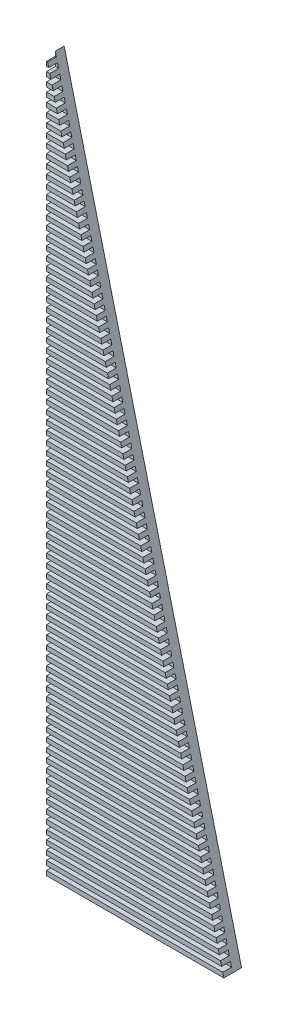
SolidWorks part; units mm, degrees
ref_plane "Front Plane" through (0, 0, 0) normal (0, 0, 1) x (1, 0, 0)
ref_plane "Top Plane" through (0, 0, 0) normal (0, 1, 0) x (1, 0, 0)
ref_plane "Right Plane" through (0, 0, 0) normal (1, 0, 0) x (0, 0, -1)
sketch "Sketch2" plane through (0, 0, 0) normal (0, 0, 1) x (1, 0, 0)
  line L0 (-53.1415, -19.5554) -> (-13.1415, -19.5554)
  line L1 (-53.1415, -19.5554) -> (-53.1415, 140.4446)
  line L2 (-53.1415, 140.4446) -> (-13.1415, -19.5554)
  dimension "D1" = 40
  dimension "D2" = 160
extrude "Boss-Extrude4" add sketch "Sketch2" along normal blind 2
sketch "Sketch4" plane through (0, 0, 2) normal (0, 0, 1) x (1, 0, 0)
  line L0 (-53.1415, -19.5554) -> (-13.1415, -19.5554)
  line L1 (-13.1415, -19.5554) -> (-53.1415, 140.4446)
  line L2 (-53.1415, 140.4446) -> (-53.1415, -19.5554)
  line L3 (-53.1415, -18.5554) -> (-13.3915, -18.5554)
  line L4 (-53.1415, -17.5554) -> (-13.6415, -17.5554)
  line L5 (-53.1415, -16.5554) -> (-13.8915, -16.5554)
  line L6 (-53.1415, -15.5554) -> (-14.1415, -15.5554)
  line L7 (-53.1415, -14.5554) -> (-14.3915, -14.5554)
  line L8 (-53.1415, -13.5554) -> (-14.6415, -13.5554)
  line L9 (-53.1415, -12.5554) -> (-14.8915, -12.5554)
  line L10 (-53.1415, -11.5554) -> (-15.1415, -11.5554)
  line L11 (-53.1415, -10.5554) -> (-15.3915, -10.5554)
  line L12 (-53.1415, -9.5554) -> (-15.6415, -9.5554)
  line L13 (-53.1415, -8.5554) -> (-15.8915, -8.5554)
  line L14 (-53.1415, -7.5554) -> (-16.1415, -7.5554)
  line L15 (-53.1415, -6.5554) -> (-16.3915, -6.5554)
  line L16 (-53.1415, -5.5554) -> (-16.6415, -5.5554)
  line L17 (-53.1415, -4.5554) -> (-16.8915, -4.5554)
  line L18 (-53.1415, -3.5554) -> (-17.1415, -3.5554)
  line L19 (-53.1415, -2.5554) -> (-17.3915, -2.5554)
  line L20 (-53.1415, -1.5554) -> (-17.6415, -1.5554)
  line L21 (-53.1415, -0.5554) -> (-17.8915, -0.5554)
  line L22 (-53.1415, 0.4446) -> (-18.1415, 0.4446)
  line L23 (-53.1415, 1.4446) -> (-18.3915, 1.4446)
  line L24 (-53.1415, 2.4446) -> (-18.6415, 2.4446)
  line L25 (-53.1415, 3.4446) -> (-18.8915, 3.4446)
  line L26 (-53.1415, 4.4446) -> (-19.1415, 4.4446)
  line L27 (-53.1415, 5.4446) -> (-19.3915, 5.4446)
  line L28 (-53.1415, 6.4446) -> (-19.6415, 6.4446)
  line L29 (-53.1415, 7.4446) -> (-19.8915, 7.4446)
  line L30 (-53.1415, 8.4446) -> (-20.1415, 8.4446)
  line L31 (-53.1415, 9.4446) -> (-20.3915, 9.4446)
  line L32 (-53.1415, 10.4446) -> (-20.6415, 10.4446)
  line L33 (-53.1415, 11.4446) -> (-20.8915, 11.4446)
  line L34 (-53.1415, 12.4446) -> (-21.1415, 12.4446)
  line L35 (-53.1415, 13.4446) -> (-21.3915, 13.4446)
  line L36 (-53.1415, 14.4446) -> (-21.6415, 14.4446)
  line L37 (-53.1415, 15.4446) -> (-21.8915, 15.4446)
  line L38 (-53.1415, 16.4446) -> (-22.1415, 16.4446)
  line L39 (-53.1415, 17.4446) -> (-22.3915, 17.4446)
  line L40 (-53.1415, 18.4446) -> (-22.6415, 18.4446)
  line L41 (-53.1415, 19.4446) -> (-22.8915, 19.4446)
  line L42 (-53.1415, 20.4446) -> (-23.1415, 20.4446)
  line L43 (-53.1415, 21.4446) -> (-23.3915, 21.4446)
  line L44 (-53.1415, 22.4446) -> (-23.6415, 22.4446)
  line L45 (-53.1415, 23.4446) -> (-23.8915, 23.4446)
  line L46 (-53.1415, 24.4446) -> (-24.1415, 24.4446)
  line L47 (-53.1415, 25.4446) -> (-24.3915, 25.4446)
  line L48 (-53.1415, 26.4446) -> (-24.6415, 26.4446)
  line L49 (-53.1415, 27.4446) -> (-24.8915, 27.4446)
  line L50 (-53.1415, 28.4446) -> (-25.1415, 28.4446)
  line L51 (-53.1415, 29.4446) -> (-25.3915, 29.4446)
  line L52 (-53.1415, 30.4446) -> (-25.6415, 30.4446)
  line L53 (-53.1415, 31.4446) -> (-25.8915, 31.4446)
  line L54 (-53.1415, 32.4446) -> (-26.1415, 32.4446)
  line L55 (-53.1415, 33.4446) -> (-26.3915, 33.4446)
  line L56 (-53.1415, 34.4446) -> (-26.6415, 34.4446)
  line L57 (-53.1415, 35.4446) -> (-26.8915, 35.4446)
  line L58 (-53.1415, 36.4446) -> (-27.1415, 36.4446)
  line L59 (-53.1415, 37.4446) -> (-27.3915, 37.4446)
  line L60 (-53.1415, 38.4446) -> (-27.6415, 38.4446)
  line L61 (-53.1415, 39.4446) -> (-27.8915, 39.4446)
  line L62 (-53.1415, 40.4446) -> (-28.1415, 40.4446)
  line L63 (-53.1415, 41.4446) -> (-28.3915, 41.4446)
  line L64 (-53.1415, 42.4446) -> (-28.6415, 42.4446)
  line L65 (-53.1415, 43.4446) -> (-28.8915, 43.4446)
  line L66 (-53.1415, 44.4446) -> (-29.1415, 44.4446)
  line L67 (-53.1415, 45.4446) -> (-29.3915, 45.4446)
  line L68 (-53.1415, 46.4446) -> (-29.6415, 46.4446)
  line L69 (-53.1415, 47.4446) -> (-29.8915, 47.4446)
  line L70 (-53.1415, 48.4446) -> (-30.1415, 48.4446)
  line L71 (-53.1415, 49.4446) -> (-30.3915, 49.4446)
  line L72 (-53.1415, 50.4446) -> (-30.6415, 50.4446)
  line L73 (-53.1415, 51.4446) -> (-30.8915, 51.4446)
  line L74 (-53.1415, 52.4446) -> (-31.1415, 52.4446)
  line L75 (-53.1415, 53.4446) -> (-31.3915, 53.4446)
  line L76 (-53.1415, 54.4446) -> (-31.6415, 54.4446)
  line L77 (-53.1415, 55.4446) -> (-31.8915, 55.4446)
  line L78 (-53.1415, 56.4446) -> (-32.1415, 56.4446)
  line L79 (-53.1415, 57.4446) -> (-32.3915, 57.4446)
  line L80 (-53.1415, 58.4446) -> (-32.6415, 58.4446)
  line L81 (-53.1415, 59.4446) -> (-32.8915, 59.4446)
  line L82 (-53.1415, 60.4446) -> (-33.1415, 60.4446)
  line L83 (-53.1415, 61.4446) -> (-33.3915, 61.4446)
  line L84 (-53.1415, 62.4446) -> (-33.6415, 62.4446)
  line L85 (-53.1415, 63.4446) -> (-33.8915, 63.4446)
  line L86 (-53.1415, 64.4446) -> (-34.1415, 64.4446)
  line L87 (-53.1415, 65.4446) -> (-34.3915, 65.4446)
  line L88 (-53.1415, 66.4446) -> (-34.6415, 66.4446)
  line L89 (-53.1415, 67.4446) -> (-34.8915, 67.4446)
  line L90 (-53.1415, 68.4446) -> (-35.1415, 68.4446)
  line L91 (-53.1415, 69.4446) -> (-35.3915, 69.4446)
  line L92 (-53.1415, 70.4446) -> (-35.6415, 70.4446)
  line L93 (-53.1415, 71.4446) -> (-35.8915, 71.4446)
  line L94 (-53.1415, 72.4446) -> (-36.1415, 72.4446)
  line L95 (-53.1415, 73.4446) -> (-36.3915, 73.4446)
  line L96 (-53.1415, 74.4446) -> (-36.6415, 74.4446)
  line L97 (-53.1415, 75.4446) -> (-36.8915, 75.4446)
  line L98 (-53.1415, 76.4446) -> (-37.1415, 76.4446)
  line L99 (-53.1415, 77.4446) -> (-37.3915, 77.4446)
  line L100 (-53.1415, 78.4446) -> (-37.6415, 78.4446)
  line L101 (-53.1415, 79.4446) -> (-37.8915, 79.4446)
  line L102 (-53.1415, 80.4446) -> (-38.1415, 80.4446)
  line L103 (-53.1415, 81.4446) -> (-38.3915, 81.4446)
  line L104 (-53.1415, 82.4446) -> (-38.6415, 82.4446)
  line L105 (-53.1415, 83.4446) -> (-38.8915, 83.4446)
  line L106 (-53.1415, 84.4446) -> (-39.1415, 84.4446)
  line L107 (-53.1415, 85.4446) -> (-39.3915, 85.4446)
  line L108 (-53.1415, 86.4446) -> (-39.6415, 86.4446)
  line L109 (-53.1415, 87.4446) -> (-39.8915, 87.4446)
  line L110 (-53.1415, 88.4446) -> (-40.1415, 88.4446)
  line L111 (-53.1415, 89.4446) -> (-40.3915, 89.4446)
  line L112 (-53.1415, 90.4446) -> (-40.6415, 90.4446)
  line L113 (-53.1415, 91.4446) -> (-40.8915, 91.4446)
  line L114 (-53.1415, 92.4446) -> (-41.1415, 92.4446)
  line L115 (-53.1415, 93.4446) -> (-41.3915, 93.4446)
  line L116 (-53.1415, 94.4446) -> (-41.6415, 94.4446)
  line L117 (-53.1415, 95.4446) -> (-41.8915, 95.4446)
  line L118 (-53.1415, 96.4446) -> (-42.1415, 96.4446)
  line L119 (-53.1415, 97.4446) -> (-42.3915, 97.4446)
  line L120 (-53.1415, 98.4446) -> (-42.6415, 98.4446)
  line L121 (-53.1415, 99.4446) -> (-42.8915, 99.4446)
  line L122 (-53.1415, 100.4446) -> (-43.1415, 100.4446)
  line L123 (-53.1415, 101.4446) -> (-43.3915, 101.4446)
  line L124 (-53.1415, 102.4446) -> (-43.6415, 102.4446)
  line L125 (-53.1415, 103.4446) -> (-43.8915, 103.4446)
  line L126 (-53.1415, 104.4446) -> (-44.1415, 104.4446)
  line L127 (-53.1415, 105.4446) -> (-44.3915, 105.4446)
  line L128 (-53.1415, 106.4446) -> (-44.6415, 106.4446)
  line L129 (-53.1415, 107.4446) -> (-44.8915, 107.4446)
  line L130 (-53.1415, 108.4446) -> (-45.1415, 108.4446)
  line L131 (-53.1415, 109.4446) -> (-45.3915, 109.4446)
  line L132 (-53.1415, 110.4446) -> (-45.6415, 110.4446)
  line L133 (-53.1415, 111.4446) -> (-45.8915, 111.4446)
  line L134 (-53.1415, 112.4446) -> (-46.1415, 112.4446)
  line L135 (-53.1415, 113.4446) -> (-46.3915, 113.4446)
  line L136 (-53.1415, 114.4446) -> (-46.6415, 114.4446)
  line L137 (-53.1415, 115.4446) -> (-46.8915, 115.4446)
  line L138 (-53.1415, 116.4446) -> (-47.1415, 116.4446)
  line L139 (-53.1415, 117.4446) -> (-47.3915, 117.4446)
  line L140 (-53.1415, 118.4446) -> (-47.6415, 118.4446)
  line L141 (-53.1415, 119.4446) -> (-47.8915, 119.4446)
  line L142 (-53.1415, 120.4446) -> (-48.1415, 120.4446)
  line L143 (-53.1415, 121.4446) -> (-48.3915, 121.4446)
  line L144 (-53.1415, 122.4446) -> (-48.6415, 122.4446)
  line L145 (-53.1415, 123.4446) -> (-48.8915, 123.4446)
  line L146 (-53.1415, 124.4446) -> (-49.1415, 124.4446)
  line L147 (-53.1415, 125.4446) -> (-49.3915, 125.4446)
  line L148 (-53.1415, 126.4446) -> (-49.6415, 126.4446)
  line L149 (-53.1415, 127.4446) -> (-49.8915, 127.4446)
  line L150 (-53.1415, 128.4446) -> (-50.1415, 128.4446)
  line L151 (-53.1415, 129.4446) -> (-50.3915, 129.4446)
  line L152 (-53.1415, 130.4446) -> (-50.6415, 130.4446)
  line L153 (-53.1415, 131.4446) -> (-50.8915, 131.4446)
  line L154 (-53.1415, 132.4446) -> (-51.1415, 132.4446)
  line L155 (-53.1415, 133.4446) -> (-51.3915, 133.4446)
  line L156 (-53.1415, 134.4446) -> (-51.6415, 134.4446)
  line L157 (-53.1415, 135.4446) -> (-51.8915, 135.4446)
  line L158 (-53.1415, 136.4446) -> (-52.1415, 136.4446)
  line L159 (-53.1415, 137.4446) -> (-52.3915, 137.4446)
  line L160 (-53.1415, 138.4446) -> (-52.6415, 138.4446)
  line L161 (-53.1415, 139.4446) -> (-52.8915, 139.4446)
  line L166 (-53.1415, 143.4446) -> (-7.1623, 143.4446) [skipped]
  line L167 (-53.1415, 142.4446) -> (-7.1623, 142.4446) [skipped]
  line L168 (-53.1415, 141.4446) -> (-7.1623, 141.4446) [skipped]
  line L169 (-53.1415, 140.4446) -> (-7.1623, 140.4446) [skipped]
  line M4 (-53.1415, -19.5554) -> (-13.1415, -19.5554)
  line M5 (-13.1415, -19.5554) -> (-53.1415, 140.4446)
  dimension "D1" = 1
  dimension "D2" = 163
extrude "Boss-Extrude6" add sketch "Sketch4" along normal blind 2 contours L3 L2 M4 M5 | L5 L2 L4 M5 | L7 L2 L6 M5 | L9 L2 L8 M5 | L11 L2 L10 M5 | L13 L2 L12 M5 | L15 L2 L14 M5 | L17 L2 L16 M5 | L19 L2 L18 M5 | L21 L2 L20 M5 | L23 L2 L22 M5 | L25 L2 L24 M5 | L27 L2 L26 M5 | L29 L2 L28 M5 | L31 L2 L30 M5 | L33 L2 L32 M5 | L35 L2 L34 M5 | L37 L2 L36 M5 | L39 L2 L38 M5 | L41 L2 L40 M5 | L43 L2 L42 M5 | L45 L2 L44 M5 | L47 L2 L46 M5 | L49 L2 L48 M5 | L51 L2 L50 M5 | L53 L2 L52 M5 | L55 L2 L54 M5 | L57 L2 L56 M5 | L59 L2 L58 M5 | L61 L2 L60 M5 | L63 L2 L62 M5 | L65 L2 L64 M5 | L67 L2 L66 M5 | L69 L2 L68 M5 | L71 L2 L70 M5 | L73 L2 L72 M5 | L75 L2 L74 M5 | L77 L2 L76 M5 | L79 L2 L78 M5 | L81 L2 L80 M5 | L83 L2 L82 M5 | L85 L2 L84 M5 | L87 L2 L86 M5 | L89 L2 L88 M5 | L91 L2 L90 M5 | L93 L2 L92 M5 | L95 L2 L94 M5 | L97 L2 L96 M5 | L99 L2 L98 M5 | L101 L2 L100 M5 | L103 L2 L102 M5 | L105 L2 L104 M5 | L107 L2 L106 M5 | L109 L2 L108 M5 | L111 L2 L110 M5 | L113 L2 L112 M5 | L115 L2 L114 M5 | L117 L2 L116 M5 | L119 L2 L118 M5 | L121 L2 L120 M5 | L123 L2 L122 M5 | L125 L2 L124 M5 | L127 L2 L126 M5 | L129 L2 L128 M5 | L131 L2 L130 M5 | L133 L2 L132 M5 | L135 L2 L134 M5 | L137 L2 L136 M5 | L139 L2 L138 M5 | L141 L2 L140 M5 | L143 L2 L142 M5 | L145 L2 L144 M5 | L147 L2 L146 M5 | L149 L2 L148 M5 | L151 L2 L150 M5 | L153 L2 L152 M5 | L155 L2 L154 M5 | L157 L2 L156 M5 | L159 L2 L158 M5 | L161 L2 L160 M5
